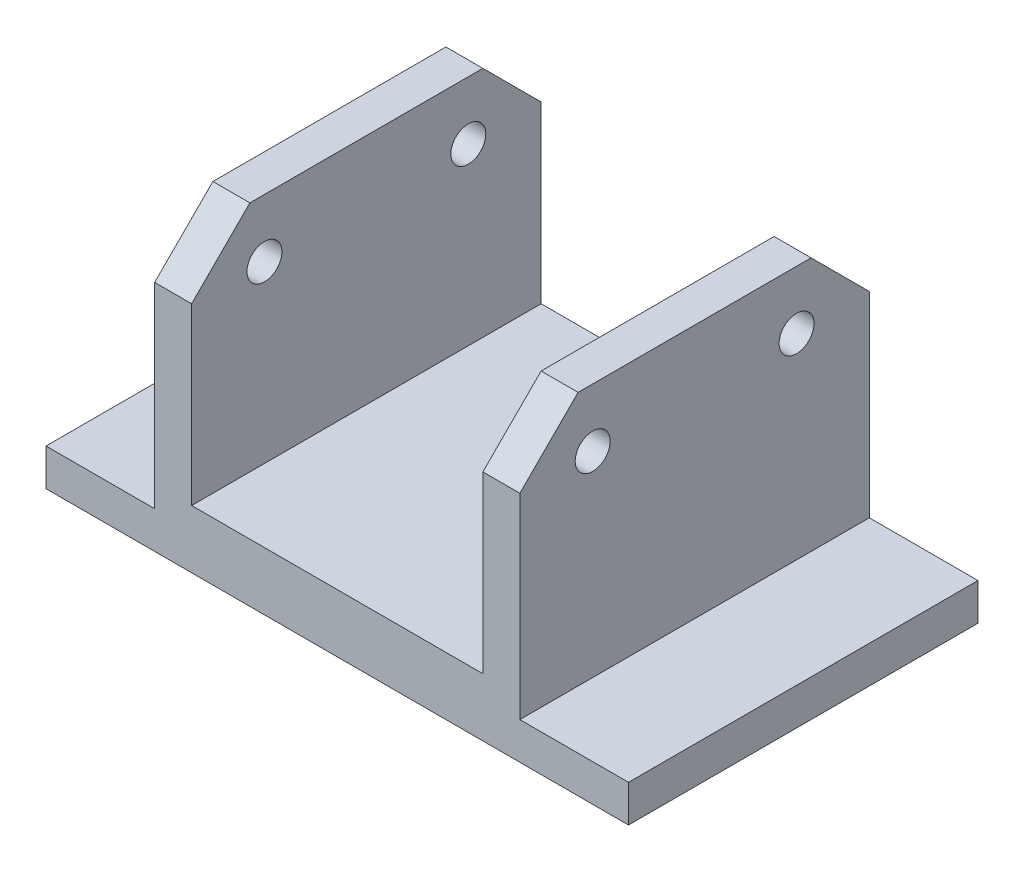
SolidWorks part; units mm, degrees
ref_plane "Plano frontal" through (0, 0, 0) normal (0, 0, 1) x (1, 0, 0)
ref_plane "Plano superior" through (0, 0, 0) normal (0, 1, 0) x (1, 0, 0)
ref_plane "Plano direito" through (0, 0, 0) normal (1, 0, 0) x (0, 0, -1)
sketch "Esboço1" plane through (0, 0, 0) normal (0, 0, 1) x (1, 0, 0)
  line L0 (0, 0) -> (0, 129.2931) construction
  line L1 (-100, 0) -> (100, 0)
  line L2 (100, 0) -> (100, 12.7)
  line L3 (100, 12.7) -> (62.7, 12.7)
  line L4 (62.7, 12.7) -> (62.7, 100)
  line L5 (62.7, 100) -> (50, 100)
  line L6 (50, 100) -> (50, 20)
  line L7 (50, 20) -> (-50, 20)
  line L8 (-50, 100) -> (-50, 20)
  line L9 (-62.7, 100) -> (-50, 100)
  line L10 (-62.7, 12.7) -> (-62.7, 100)
  line L11 (-100, 12.7) -> (-62.7, 12.7)
  line L12 (-100, 0) -> (-100, 12.7)
  point P11 (0, 20)
  dimension "D1" = 12.7
  dimension "D2" = 100
  dimension "D3" = 200
  dimension "D4" = 12.7
  dimension "D5" = 80
  dimension "D6" = 100
extrude "Ressalto-extrusão1" add sketch "Esboço1" along normal mid plane 120
chamfer "Chanfro1" distance 20 angle 45 4 edges at (56.35, 100, -60) (56.35, 100, 60) (-56.35, 100, -60) (-56.35, 100, 60)
sketch "Esboço2" plane through (62.7, 0, 0) normal (1, 0, 0) x (0, 0, -1)
  line L0 (0, 0) -> (0, 100) construction
  line L1 (-40, 100) -> (40, 100) construction
  circle A0 centre (-35, 80) radius 6
  circle A1 centre (35, 80) radius 6
  point P9 (-23.436, 100)
  point P10 (-22.6348, 100)
  dimension "D2" = 20
  dimension "D3" = 12
  dimension "D1" = 35
extrude "Corte-extrusão1" cut sketch "Esboço2" against normal through all
